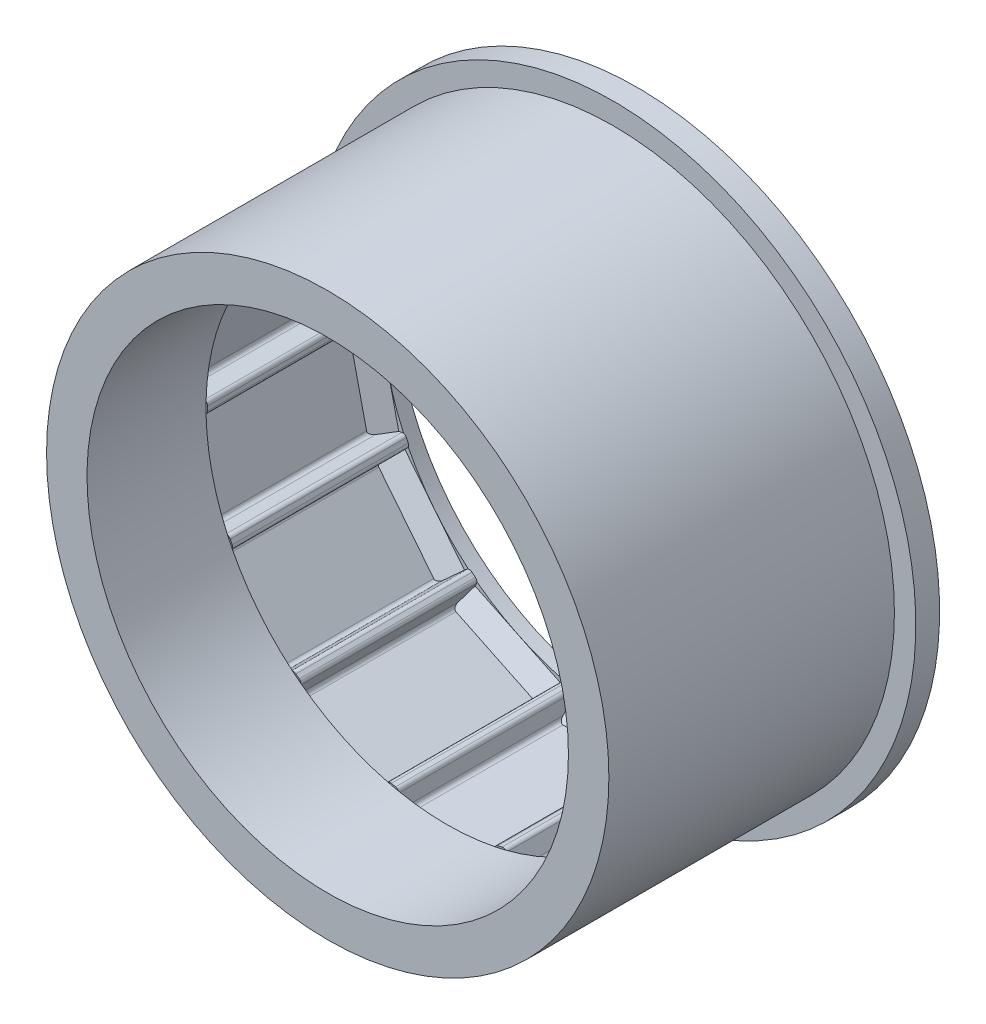
SolidWorks part; units mm, degrees
ref_plane "正面" through (0, 0, 0) normal (0, 0, 1) x (1, 0, 0)
ref_plane "平面" through (0, 0, 0) normal (0, 1, 0) x (1, 0, 0)
ref_plane "右側面" through (0, 0, 0) normal (1, 0, 0) x (0, 0, -1)
sketch "ｽｹｯﾁ1" plane through (0, 0, 0) normal (0, 0, 1) x (1, 0, 0)
  circle A0 centre (0, 0) radius 38.15 construction
  circle A1 centre (0, 0) radius 35.45
  circle A2 centre (0, 0) radius 30.15
  dimension "D1" = 76.3
  dimension "D2" = 2.7
  dimension "D3" = 5.3
extrude "ﾎﾞｽ - 押し出し1" add sketch "ｽｹｯﾁ1" along normal blind 22.2
sketch "ｽｹｯﾁ2" plane through (0, 0, 22.2) normal (0, 0, 1) x (1, 0, 0)
  line L1 (-6.05, 27.95) -> (6.05, 27.95)
  line L2 (-6.05, 27.95) -> (-6.05, 32.35)
  line L3 (-6.05, 32.35) -> (6.05, 32.35)
  line L4 (6.05, 27.95) -> (6.05, 32.35)
  line L5 (-6.05, 27.95) -> (6.05, 32.35) construction
  line L6 (-6.05, 32.35) -> (6.05, 27.95) construction
  circle A0 centre (0, 0) radius 30.15 construction
  point P0 (0, 30.15)
  dimension "D1" = 2.2
  dimension "D2" = 12.1
extrude "ｶｯﾄ - 押し出し1" cut sketch "ｽｹｯﾁ2" against normal through all
fillet "ﾌｨﾚｯﾄ1" radius 0.5 2 edges at (6.05, 29.5368, 11.1) (-6.05, 29.5368, 11.1)
fillet "ﾌｨﾚｯﾄ2" radius 0.5 2 edges at (6.05, 32.35, 11.1) (-6.05, 32.35, 11.1)
pattern_circular "円形ﾊﾟﾀｰﾝ1" count 14 over 360 about axis through (0, 0, 0) along (0, 0, 1) of "ｶｯﾄ - 押し出し1", "ﾌｨﾚｯﾄ1", "ﾌｨﾚｯﾄ2"
sketch "ｽｹｯﾁ3" plane through (0, 0, 0) normal (0, 0, -1) x (-1, 0, 0)
  circle A1 centre (0, 0) radius 30.35
  circle A2 centre (0, 0) radius 35.45 construction
  circle A3 centre (0, 0) radius 35.45
extrude "ﾎﾞｽ - 押し出し2" add sketch "ｽｹｯﾁ3" along normal blind 1.8
sketch "ｽｹｯﾁ4" plane through (0, 0, 22.2) normal (0, 0, 1) x (1, 0, 0)
  circle A1 centre (0, 0) radius 30.35
  circle A4 centre (0, 0) radius 35.45 construction
  circle A5 centre (0, 0) radius 35.45
extrude "ﾎﾞｽ - 押し出し3" add sketch "ｽｹｯﾁ4" along normal blind 15
sketch "ｽｹｯﾁ6" plane through (0, 0, 0) normal (1, 0, 0) x (0, 0, -1)
  line L2 (0, -29.658) -> (0, -30.35) construction
  line L3 (0, -30.35) -> (0, -33.35)
  line L4 (0, -33.35) -> (-3, -33.35)
  line L5 (-3, -33.35) -> (0, -30.35)
  dimension "D1" = 3
extrude "ﾎﾞｽ - 押し出し4" add sketch "ｽｹｯﾁ6" along normal mid plane 14
pattern_circular "円形ﾊﾟﾀｰﾝ2" count 14 over 360 about axis through (0, 0, 0) along (0, 0, 1) of "ﾎﾞｽ - 押し出し4"
sketch "ｽｹｯﾁ7" plane through (0, 0, -1.8) normal (0, 0, -1) x (-1, 0, 0)
  circle A0 centre (0, 0) radius 35.45 construction
  circle A1 centre (0, 0) radius 35.45
  circle A2 centre (0, 0) radius 38.15
  dimension "D1" = 76.3
extrude "ﾎﾞｽ - 押し出し6" add sketch "ｽｹｯﾁ7" against normal blind 3
